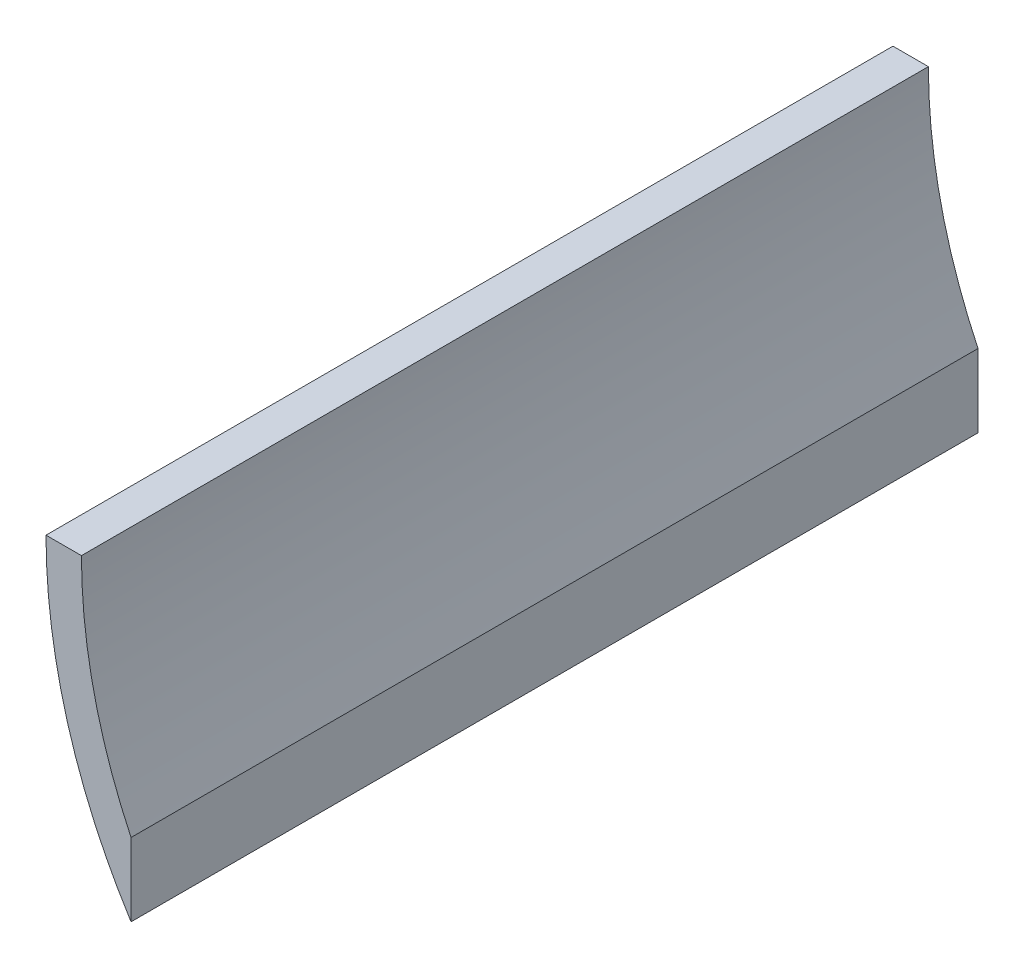
SolidWorks part; units mm, degrees
material "that blue high density foam"
ref_plane "Front" through (0, 0, 0) normal (0, 0, 1) x (1, 0, 0)
ref_plane "Top" through (0, 0, 0) normal (0, 1, 0) x (1, 0, 0)
ref_plane "Right" through (0, 0, 0) normal (1, 0, 0) x (0, 0, -1)
sketch "Sketch1" plane through (0, 0, 0) normal (0, 0, 1) x (1, 0, 0)
  line L2 (-82, -47.1761) -> (-82, -67.7866)
  line L3 (-96, 14.7134) -> (-106, 14.7134)
  line L5 (-82, -67.7866) -> (-82, -25.6187) construction
  line L6 (-96, 35.7134) -> (-96, 14.7134) construction
  arc A0 (-106, 14.7134) -> (-82, -67.7866) centre (47.7969, 14.7134) ccw construction
  arc A1 (-106, 14.7134) -> (-82, -67.7866) centre (47.7969, 14.7134) ccw
  arc A2 (-96, 14.7134) -> (-82, -47.1761) centre (47.7969, 14.7134) ccw
  dimension "D1" = 10
extrude "Boss-Extrude1" add sketch "Sketch1" along normal up to surface (239 mm away)
